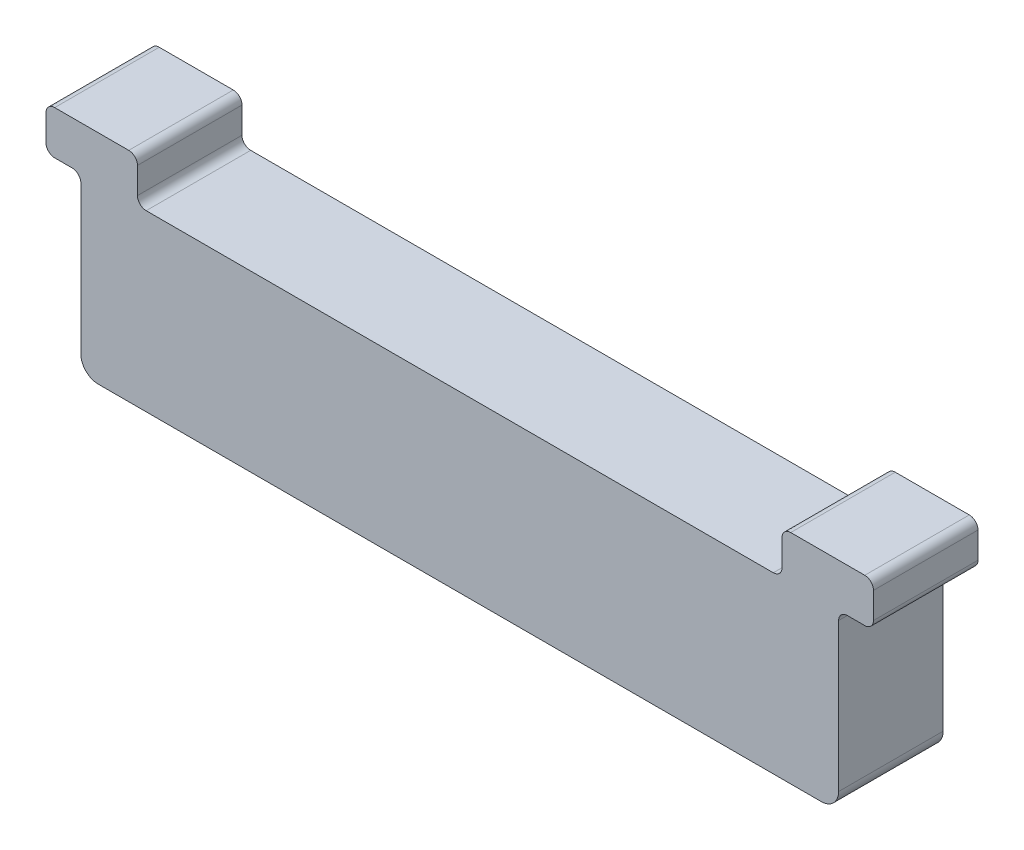
SolidWorks part; units mm, degrees
ref_plane "Plane1" through (0, 0, 0) normal (0, 0, 1) x (1, 0, 0)
ref_plane "Plane2" through (0, 0, 0) normal (0, 1, 0) x (1, 0, 0)
ref_plane "Plane3" through (0, 0, 0) normal (1, 0, 0) x (0, 0, -1)
sketch "Sketch1" plane through (0, 0, 0) normal (0, 0, 1) x (1, 0, 0)
  line L0 (0, 0) -> (0, 10) construction
  line L1 (-20.75, 0) -> (20.75, 0)
  line L2 (23.75, 10.5) -> (23.75, 12)
  line L3 (23.25, 12.5) -> (19, 12.5)
  line L4 (18.5, 12) -> (18.5, 10.5)
  line L5 (18, 10) -> (-18, 10)
  line L6 (-18.5, 12) -> (-18.5, 10.5)
  line L7 (-23.25, 12.5) -> (-19, 12.5)
  line L8 (-23.75, 10.5) -> (-23.75, 12)
  line L9 (23.25, 10) -> (22.25, 10)
  line L10 (21.75, 9.5) -> (21.75, 1)
  line L11 (-21.75, 9.5) -> (-21.75, 1)
  line L12 (-23.25, 10) -> (-22.25, 10)
  arc A0 (23.75, 12) -> (23.25, 12.5) centre (23.25, 12) ccw
  arc A1 (-23.25, 12.5) -> (-23.75, 12) centre (-23.25, 12) ccw
  arc A2 (-18.5, 12) -> (-19, 12.5) centre (-19, 12) ccw
  arc A3 (-18.5, 10.5) -> (-18, 10) centre (-18, 10.5) ccw
  arc A4 (18.5, 10.5) -> (18, 10) centre (18, 10.5) cw
  arc A5 (19, 12.5) -> (18.5, 12) centre (19, 12) ccw
  arc A6 (21.75, 1) -> (20.75, 0) centre (20.75, 1) cw
  arc A7 (-21.75, 1) -> (-20.75, 0) centre (-20.75, 1) ccw
  arc A8 (23.25, 10) -> (23.75, 10.5) centre (23.25, 10.5) ccw
  arc A9 (22.25, 10) -> (21.75, 9.5) centre (22.25, 9.5) ccw
  arc A10 (-21.75, 9.5) -> (-22.25, 10) centre (-22.25, 9.5) ccw
  arc A11 (-23.25, 10) -> (-23.75, 10.5) centre (-23.25, 10.5) cw
  point P13 (23.75, 12.5)
  point P16 (-23.75, 12.5)
  point P19 (-18.5, 12.5)
  point P22 (-18.5, 10)
  point P25 (18.5, 10)
  point P28 (18.5, 12.5)
  point P29 (21.75, 0)
  point P33 (-21.75, 0)
  point P41 (23.75, 10)
  point P44 (21.75, 10)
  point P47 (-21.75, 10)
  point P50 (-23.75, 10)
  dimension "D5" = 0.5
  dimension "D7" = 1
  dimension "D8" = 0.5
  dimension "D1" = 47.5
  dimension "D2" = 10
  dimension "D3" = 12.5
  dimension "D4" = 37
  dimension "D6" = 43.5
  dimension "D9" = 2
extrude "Extrude1" add sketch "Sketch1" along normal blind 6
